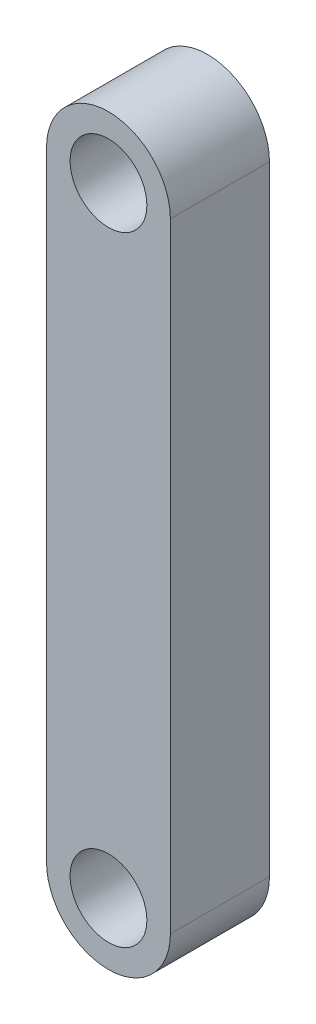
SolidWorks part; units mm, degrees
ref_plane "前视基准面" through (0, 0, 0) normal (0, 0, 1) x (1, 0, 0)
ref_plane "上视基准面" through (0, 0, 0) normal (0, 1, 0) x (1, 0, 0)
ref_plane "右视基准面" through (0, 0, 0) normal (1, 0, 0) x (0, 0, -1)
sketch "草图1" plane through (0, 0, 0) normal (0, 0, 1) x (1, 0, 0)
  line L0 (0, 0) -> (0, 27.6862) construction
  line L2 (-2.5, -12.5) -> (-2.5, 12.5)
  line L4 (2.5, -12.5) -> (2.5, 12.5)
  line L5 (0, 0) -> (26.5177, 0) construction
  arc A0 (-2.5, 12.5) -> (2.5, 12.5) centre (0, 12.5) cw
  arc A1 (-2.5, -12.5) -> (2.5, -12.5) centre (0, -12.5) ccw
  circle A2 centre (0, 12.5) radius 1.55
  circle A3 centre (0, -12.5) radius 1.55
  dimension "D1" = 2.5
  dimension "D2" = 3.1
  dimension "D3" = 25
extrude "凸台-拉伸1" add sketch "草图1" along normal blind 4
